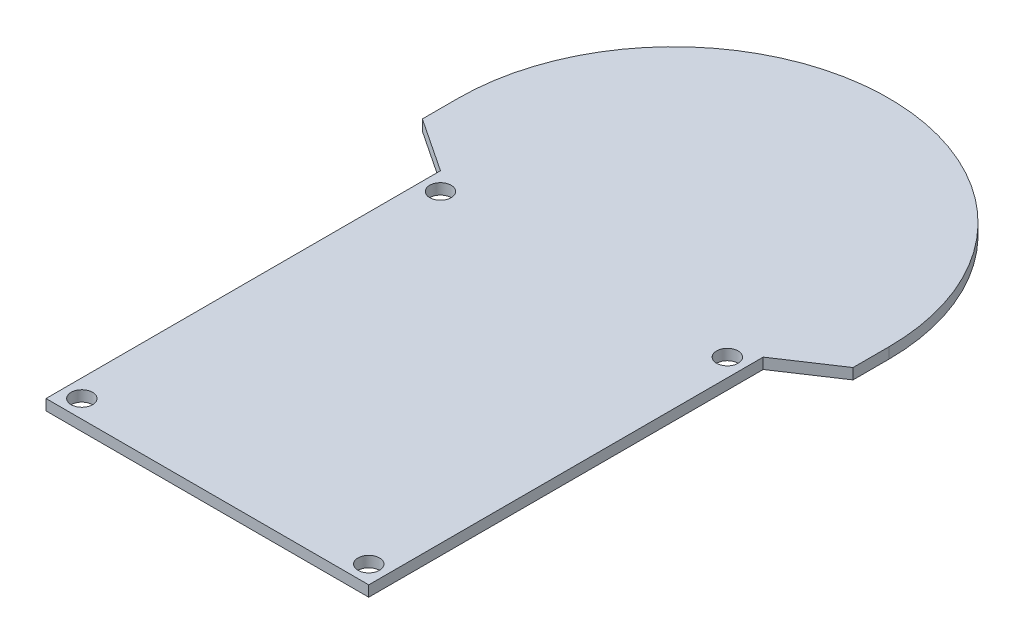
SolidWorks part; units mm, degrees
ref_plane "Front Plane" through (0, 0, 0) normal (0, 0, 1) x (1, 0, 0)
ref_plane "Top Plane" through (0, 0, 0) normal (0, 1, 0) x (1, 0, 0)
ref_plane "Right Plane" through (0, 0, 0) normal (1, 0, 0) x (0, 0, -1)
sketch "Sketch1" plane through (0, 0, 0) normal (0, 1, 0) x (1, 0, 0)
  line L0 (-15, -22.5) -> (-15, 79.9562) construction
  line L1 (-45.021, 42.5) -> (-45.021, 37.5)
  line L2 (15.021, 42.5) -> (15.021, 37.5)
  line L3 (-37.5, -22.5) -> (-37.5, 32.5)
  line L4 (15.021, 37.5) -> (7.5, 32.5)
  line L5 (7.5, -22.5) -> (7.5, 32.5)
  line L8 (-45.021, 37.5) -> (-37.5, 32.5)
  line L13 (-37.5, -22.5) -> (7.5, -22.5)
  arc A0 (15.021, 42.5) -> (-45.021, 42.5) centre (-15, 42.5) ccw
  point P3 (0, 0)
  dimension "D1" = 55
  dimension "D2" = 45
  dimension "D4" = 5
extrude "Boss-Extrude1" add sketch "Sketch1" along normal blind 1.5
sketch "Sketch2" plane through (0, 1.5, 0) normal (0, 1, 0) x (1, 0, 0)
  line L0 (-37.5, 32.5) -> (-37.5, -22.5) construction
  line L1 (-15, 72.521) -> (-15, 0) construction
  line L2 (-35, -22.5) -> (-14.3955, -22.5) construction
  circle A0 centre (-35, 30) radius 1.5
  circle A1 centre (-35, -20) radius 1.5
  arc A3 (15.021, 42.5) -> (-45.021, 42.5) centre (-15, 42.5) ccw construction
  circle A4 centre (5, -20) radius 1.5
  circle A5 centre (5, 30) radius 1.5
  dimension "D1" = 3
  dimension "D4" = 3
  dimension "D2" = 2.5
  dimension "D5" = 2.5
  dimension "D6" = 2.5
extrude "Cut-Extrude1" cut sketch "Sketch2" against normal through all
